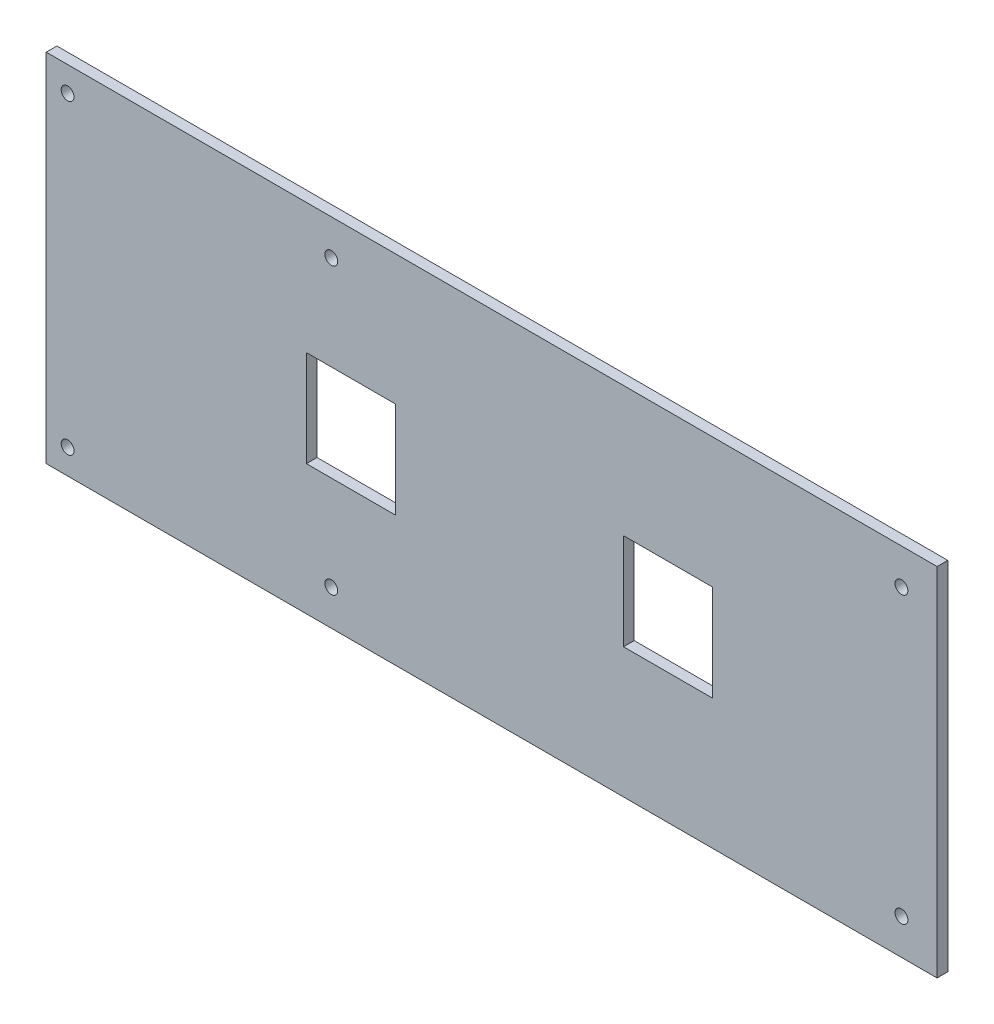
SolidWorks part; units mm, degrees
material "PMMA laser cult panels"
ref_plane "Front Plane" through (0, 0, 0) normal (0, 0, 1) x (1, 0, 0)
ref_plane "Top Plane" through (0, 0, 0) normal (0, 1, 0) x (1, 0, 0)
ref_plane "Right Plane" through (0, 0, 0) normal (1, 0, 0) x (0, 0, -1)
sketch "Sketch1" plane through (0, 0, 0) normal (0, 0, 1) x (1, 0, 0)
  line L1 (0, 0) -> (250, 0)
  line L2 (0, 0) -> (0, 100)
  line L3 (0, 100) -> (250, 100)
  line L4 (250, 0) -> (250, 100)
  dimension "D1" = 250
  dimension "D2" = 100
extrude "Boss-Extrude1" add sketch "Sketch1" along normal blind 3
sketch "Sketch2" plane through (0, 0, 3) normal (0, 0, 1) x (1, 0, 0)
  line L0 (0, 0) -> (250, 0) construction
  line L1 (250, 100) -> (0, 100) construction
  line L2 (0, 100) -> (0, 0) construction
  circle A0 centre (6, 93) radius 1.8
  circle A1 centre (80, 90) radius 1.8
  circle A2 centre (240, 90) radius 1.8
  circle A3 centre (240, 10) radius 1.8
  circle A4 centre (80, 10) radius 1.8
  circle A5 centre (6, 7) radius 1.8
  dimension "D6" = 10
  dimension "D7" = 10
  dimension "D8" = 3.6
  dimension "D1" = 7
  dimension "D2" = 7
  dimension "D3" = 6
  dimension "D4" = 80
  dimension "D5" = 240
extrude "Cut-Extrude1" cut sketch "Sketch2" against normal through all
sketch "Sketch3" plane through (0, 0, 3) normal (0, 0, 1) x (1, 0, 0)
  line L0 (0, 100) -> (0, 0) construction
  line L1 (73, 63.5) -> (98, 63.5)
  line L2 (73, 63.5) -> (73, 36.5)
  line L3 (73, 36.5) -> (98, 36.5)
  line L4 (98, 63.5) -> (98, 36.5)
  line L5 (162, 63.5) -> (187, 63.5)
  line L6 (162, 63.5) -> (162, 36.5)
  line L7 (162, 36.5) -> (187, 36.5)
  line L8 (187, 63.5) -> (187, 36.5)
  line L9 (250, 100) -> (0, 100) construction
  dimension "D1" = 73
  dimension "D2" = 98
  dimension "D3" = 162
  dimension "D4" = 187
  dimension "D5" = 36.5
  dimension "D6" = 63.5
extrude "Cut-Extrude2" cut sketch "Sketch3" against normal through all
